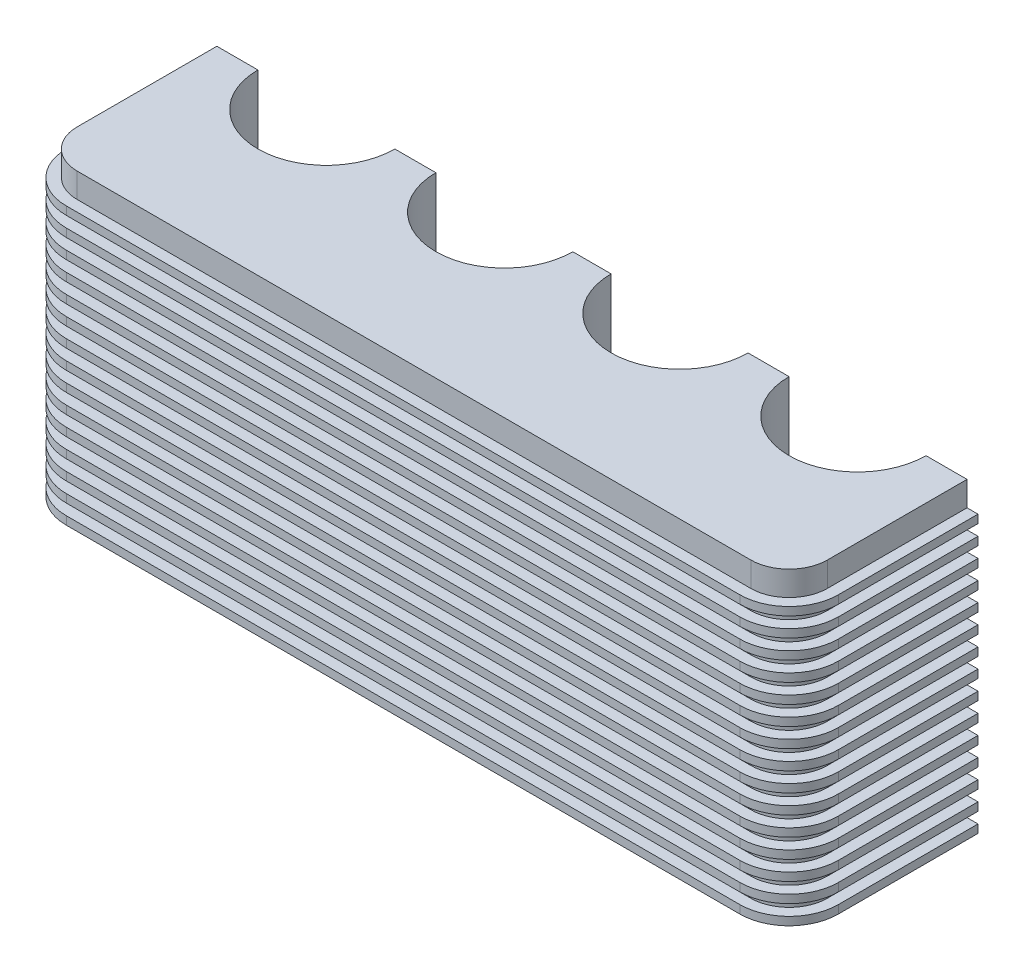
SolidWorks part; units mm, degrees
ref_plane "Front Plane" through (0, 0, 0) normal (0, 0, 1) x (1, 0, 0)
ref_plane "Top Plane" through (0, 0, 0) normal (0, 1, 0) x (1, 0, 0)
ref_plane "Right Plane" through (0, 0, 0) normal (1, 0, 0) x (0, 0, -1)
sketch "Sketch1" plane through (0, 0, 0) normal (0, 1, 0) x (1, 0, 0)
  line L0 (7, 0) -> (-7, 0)
  line L1 (-72, 0) -> (-57, 0)
  line L2 (-122, 0) -> (-137, 0)
  line L3 (-137, 0) -> (-137, -51)
  line L4 (-123, -65) -> (123, -65)
  line L5 (0, -65) -> (0, 0) construction
  line L6 (72, 0) -> (57, 0)
  line L7 (122, 0) -> (137, 0)
  line L8 (137, 0) -> (137, -51)
  circle A0 centre (-32, 0) radius 25
  circle A1 centre (-97, 0) radius 25
  arc A2 (-137, -51) -> (-123, -65) centre (-123, -51) ccw
  arc A3 (137, -51) -> (123, -65) centre (123, -51) cw
  circle A4 centre (32, 0) radius 25
  circle A5 centre (97, 0) radius 25
  point P4 (0, 0)
  point P29 (-123, -132.9613)
  point P30 (0, -101.9608)
  point P31 (0, -103.9371)
  dimension "D1" = 50
  dimension "D2" = 14
  dimension "D3" = 15
  dimension "D4" = 7
  dimension "D5" = 15
  dimension "D6" = 65
extrude "Boss-Extrude1" add sketch "Sketch1" along normal blind 110 contours L4 L5 L0 A0 L1 A1 L2 L3 A2 | L5 L4 A3 L8 L7 A5 L6 A4 L0
sketch "Sketch2" plane through (0, 0, 0) normal (0, -1, 0) x (1, 0, 0)
  line L0 (141, 0) -> (141, 51)
  line L1 (123, 69) -> (-123, 69)
  line L2 (-141, 51) -> (-141, 0)
  line L3 (-137, 0) -> (-141, 0)
  line L4 (137, 0) -> (141, 0)
  line L8 (123, 65) -> (-123, 65)
  line L9 (-137, 51) -> (-137, 0)
  line L10 (-137, 0) -> (-122, 0)
  line L11 (-72, 0) -> (-57, 0)
  line L12 (-7, 0) -> (7, 0)
  line L13 (57, 0) -> (72, 0)
  line L14 (122, 0) -> (137, 0)
  line L15 (137, 0) -> (137, 51)
  line L16 (123, 65) -> (-123, 65)
  line L17 (-137, 51) -> (-137, 0)
  line L18 (-137, 0) -> (-122, 0)
  line L19 (-72, 0) -> (-57, 0)
  line L20 (-7, 0) -> (7, 0)
  line L21 (57, 0) -> (72, 0)
  line L22 (122, 0) -> (137, 0)
  line L23 (137, 0) -> (137, 51)
  arc A0 (141, 51) -> (123, 69) centre (123, 51) ccw
  arc A1 (-123, 69) -> (-141, 51) centre (-123, 51) ccw
  arc A6 (-123, 65) -> (-137, 51) centre (-123, 51) ccw
  arc A7 (-72, 0) -> (-122, 0) centre (-97, 0) ccw
  arc A8 (-7, 0) -> (-57, 0) centre (-32, 0) ccw
  arc A9 (57, 0) -> (7, 0) centre (32, 0) ccw
  arc A10 (122, 0) -> (72, 0) centre (97, 0) ccw
  arc A11 (137, 51) -> (123, 65) centre (123, 51) ccw
  arc A12 (-123, 65) -> (-137, 51) centre (-123, 51) ccw
  arc A13 (-72, 0) -> (-122, 0) centre (-97, 0) ccw
  arc A14 (-7, 0) -> (-57, 0) centre (-32, 0) ccw
  arc A15 (57, 0) -> (7, 0) centre (32, 0) ccw
  arc A16 (122, 0) -> (72, 0) centre (97, 0) ccw
  arc A17 (137, 51) -> (123, 65) centre (123, 51) ccw
  line M15 (123, 65) -> (-123, 65)
  arc M16 (-123, 65) -> (-137, 51) centre (-123, 51) ccw
  line M17 (-137, 51) -> (-137, 0)
  line M27 (137, 0) -> (137, 51)
  arc M28 (137, 51) -> (123, 65) centre (123, 51) ccw
  dimension "D1" = 0
  dimension "D2" = 4
extrude "Boss-Extrude2" add sketch "Sketch2" against normal blind 3 contours L1 A1 L2 L3 L4 L0 A0 M17 M16 M15 M28 M27
pattern_linear "LPattern5" count 15 spacing 7 along (0, 1, 0) of "Boss-Extrude2"
